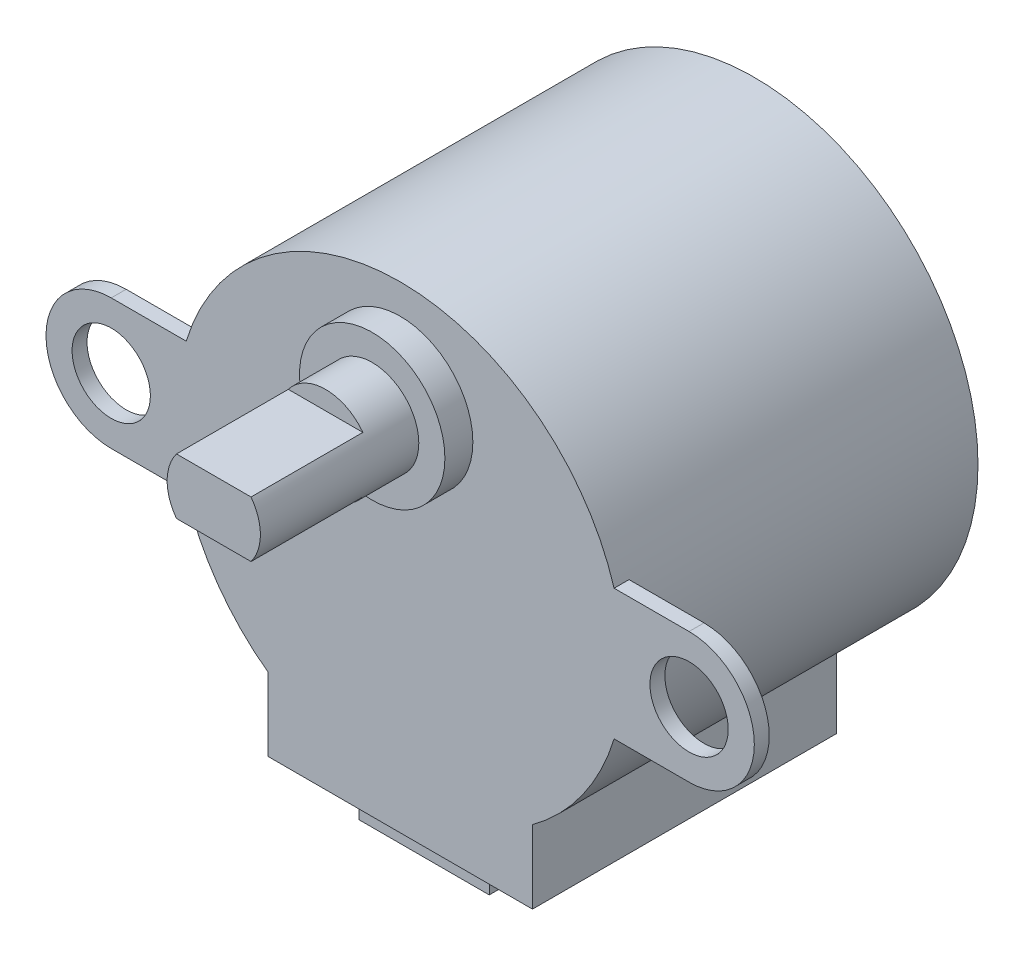
SolidWorks part; units mm, degrees
ref_plane "Front Plane" through (0, 0, 0) normal (0, 0, 1) x (1, 0, 0)
ref_plane "Top Plane" through (0, 0, 0) normal (0, 1, 0) x (1, 0, 0)
ref_plane "Right Plane" through (0, 0, 0) normal (1, 0, 0) x (0, 0, -1)
sketch "Sketch1" plane through (0, 0, 0) normal (0, 0, 1) x (1, 0, 0)
  circle A0 centre (0, 0) radius 12
  dimension "D1" = 24
extrude "Boss-Extrude1" add sketch "Sketch1" along normal blind 19
sketch "Sketch2" plane through (0, 0, 19) normal (0, 0, 1) x (1, 0, 0)
  line L0 (0, -1.8004) -> (0, -4.5993) construction
  circle A0 centre (0, 6.5) radius 3.9
  point P4 (0, 0)
  dimension "D1" = 7.8
  dimension "D2" = 6.5
extrude "Boss-Extrude2" add sketch "Sketch2" along normal blind 1.5
sketch "Sketch3" plane through (0, 0, 19) normal (0, 0, 1) x (1, 0, 0)
  line L0 (-15.5, 0) -> (15.5, 0) construction
  line L1 (-15.5, 3.5) -> (15.5, 3.5)
  line L2 (-15.5, -3.5) -> (15.5, -3.5)
  arc A0 (-15.5, 3.5) -> (-15.5, -3.5) centre (-15.5, 0) ccw
  arc A1 (15.5, -3.5) -> (15.5, 3.5) centre (15.5, 0) ccw
  circle A2 centre (-15.5, 0) radius 2.1
  circle A3 centre (15.5, 0) radius 2.1
  point P2 (0, 0)
  dimension "D2" = 3.5
  dimension "D3" = 4.2
  dimension "D4" = 4.2
  dimension "D1" = 31
extrude "Boss-Extrude3" add sketch "Sketch3" against normal blind 0.8
sketch "Sketch4" plane through (0, 0, 20.5) normal (0, 0, 1) x (1, 0, 0)
  circle A0 centre (0, 6.5) radius 2.5
  circle A1 centre (0, 6.5) radius 3.9
  circle A2 centre (0, 6.5) radius 3.9
  dimension "D2" = 5
  dimension "D1" = 0
extrude "Boss-Extrude4" add sketch "Sketch4" along normal blind 8.5 contours A0
sketch "Sketch5" plane through (0, 0, 29) normal (0, 0, 1) x (1, 0, 0)
  line L0 (0, 6.65) -> (0, 12.5573) construction
  line L1 (2, 8) -> (-2, 8)
  line L2 (-2, 5) -> (2, 5)
  circle A0 centre (0, 6.5) radius 2.5 construction
  circle A1 centre (0, 6.5) radius 2.5 construction
  circle A3 centre (0, 6.5) radius 2.5
  circle A4 centre (0, 6.5) radius 2.5
  point P11 (0, 9)
  point P12 (0, 4)
  circle M5 centre (0, 6.5) radius 2.5
  dimension "D1" = 1
  dimension "D2" = 1
  dimension "D3" = 0
extrude "Cut-Extrude2" cut sketch "Sketch5" against normal blind 6 contours L0 L1 M5 | L1 L0 A4 | L0 L2 M5 | L0 A4 L2
sketch "Sketch6" plane through (0, 0, 0) normal (0, 1, 0) x (1, 0, 0)
  line L0 (-11.4782, -19) -> (11.4782, -19) construction
  line L1 (0, -29.4859) -> (0, -24.006) construction
  line L2 (-7.1, -19) -> (7.1, -19)
  line L3 (-7.1, -19) -> (-7.1, -2.7)
  line L4 (-7.1, -2.7) -> (7.1, -2.7)
  line L5 (7.1, -19) -> (7.1, -2.7)
  point P7 (0, -2.7)
  dimension "D1" = 16.3
  dimension "D2" = 14.2
extrude "Boss-Extrude5" add sketch "Sketch6" against normal blind 13.6
sketch "Sketch7" plane through (0, -13.6, 0) normal (0, -1, 0) x (1, 0, 0)
  line L0 (-7.1, 19) -> (7.1, 19) construction
  line L1 (-3.7195, 16.5) -> (3.2805, 16.5)
  line L2 (-3.7195, 16.5) -> (-3.7195, 17.5)
  line L3 (-3.7195, 17.5) -> (3.2805, 17.5)
  line L4 (3.2805, 16.5) -> (3.2805, 17.5)
  line L5 (-3.7195, 16.5) -> (3.2805, 17.5) construction
  line L6 (-3.7195, 17.5) -> (3.2805, 16.5) construction
  point P0 (-0.2195, 17)
  dimension "D1" = 1
  dimension "D2" = 1.5
  dimension "D3" = 7
extrude "Boss-Extrude6" add sketch "Sketch7" along normal blind 2
